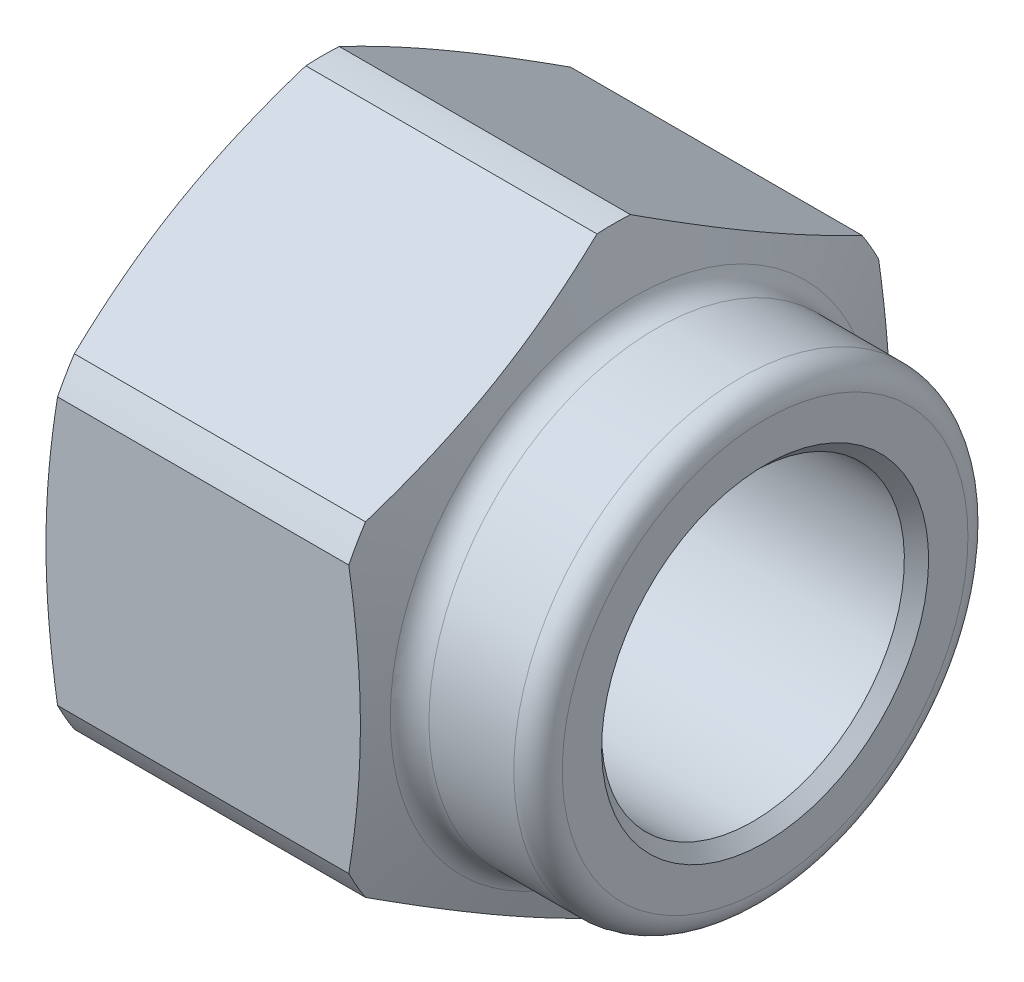
SolidWorks part; units mm, degrees
material "Cast Alloy Steel"
ref_plane "Front Plane" through (0, 0, 0) normal (0, 0, 1) x (1, 0, 0)
ref_plane "Top Plane" through (0, 0, 0) normal (0, 1, 0) x (1, 0, 0)
ref_plane "Right Plane" through (0, 0, 0) normal (1, 0, 0) x (0, 0, -1)
sketch "Sketch1" plane through (0, 0, 0) normal (1, 0, 0) x (0, 0, -1)
  line L1 (0, 6.4158) -> (-5.5562, 3.2079)
  line L2 (-5.5562, 3.2079) -> (-5.5562, -3.2079)
  line L3 (-5.5562, -3.2079) -> (0, -6.4158)
  line L4 (0, -6.4158) -> (5.5562, -3.2079)
  line L5 (5.5562, -3.2079) -> (5.5562, 3.2079)
  line L6 (5.5562, 3.2079) -> (0, 6.4158)
  circle A0 centre (0, 0) radius 5.5562 construction
  dimension "D1" = 11.1125
extrude "Boss-Extrude1" add sketch "Sketch1" along normal blind 9.525
sketch "Sketch2" plane through (0, 0, 0) normal (0, 0, 1) x (1, 0, 0)
  line L0 (0, 0) -> (9.525, 0)
  line L1 (9.525, 3.2079) -> (9.525, -3.2079) construction
  line L2 (9.525, 0) -> (9.525, 3.429)
  line L3 (9.525, 3.429) -> (9.271, 3.175)
  line L4 (9.271, 3.175) -> (0.254, 3.175)
  line L5 (0.254, 3.175) -> (0, 3.429)
  line L6 (0, 3.2079) -> (0, -3.2079) construction
  line L7 (0, 3.429) -> (0, 0)
  line L8 (0, 5.5562) -> (0.2427, 6.223)
  line L9 (0, 6.4158) -> (0, 3.2079) construction
  line L10 (0.2427, 6.223) -> (6.35, 6.223)
  line L11 (6.35, 6.223) -> (6.8816, 4.7625)
  line L12 (6.8816, 4.7625) -> (9.525, 4.7625)
  line L13 (9.525, 6.4158) -> (9.525, 3.2079) construction
  line L14 (9.525, 4.7625) -> (9.525, 6.4158)
  line L15 (9.525, 6.4158) -> (0, 6.4158)
  line L16 (0, 6.4158) -> (0, 5.5562)
  dimension "D1" = 45
  dimension "D2" = 3.175
  dimension "D3" = 0.254
  dimension "D4" = 20
  dimension "D5" = 5.5562
  dimension "D6" = 6.223
  dimension "D7" = 20
  dimension "D8" = 4.7625
  dimension "D9" = 6.35
revolve "Cut-Revolve2" cut sketch "Sketch2" angle 360 about L0
fillet "Fillet1" radius 0.508 2 edges at (6.8816, -4.7625, 0) (9.525, -4.7625, 0)
